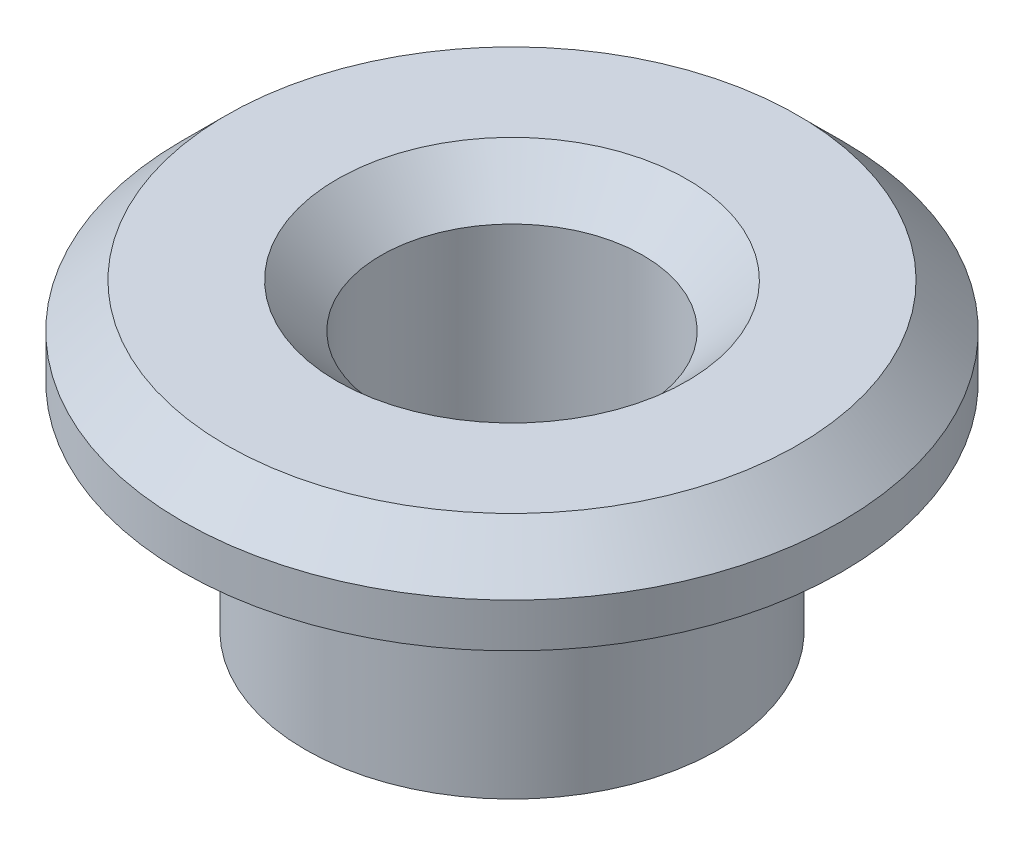
SolidWorks part; units mm, degrees
ref_plane "Front Plane" through (0, 0, 0) normal (0, 0, 1) x (1, 0, 0)
ref_plane "Top Plane" through (0, 0, 0) normal (0, 1, 0) x (1, 0, 0)
ref_plane "Right Plane" through (0, 0, 0) normal (1, 0, 0) x (0, 0, -1)
sketch "Sketch1" plane through (0, 0, 0) normal (0, 1, 0) x (1, 0, 0)
  circle A0 centre (0, 0) radius 4.7
extrude "Boss-Extrude1" add sketch "Sketch1" along normal blind 4.9
sketch "Sketch2" plane through (0, 4.9, 0) normal (0, 1, 0) x (1, 0, 0)
  circle A0 centre (0, 0) radius 7.5
extrude "Boss-Extrude2" add sketch "Sketch2" along normal blind 2
sketch "Sketch3" plane through (0, 6.9, 0) normal (0, 1, 0) x (1, 0, 0)
  circle A0 centre (0, 0) radius 2.98
extrude "Cut-Extrude1" cut sketch "Sketch3" against normal through all
chamfer "Chamfer1" distance 1 angle 45 1 edges at (0, 6.9, 2.98)
chamfer "Chamfer2" distance 1 angle 45 1 edges at (0, 6.9, 7.5)
